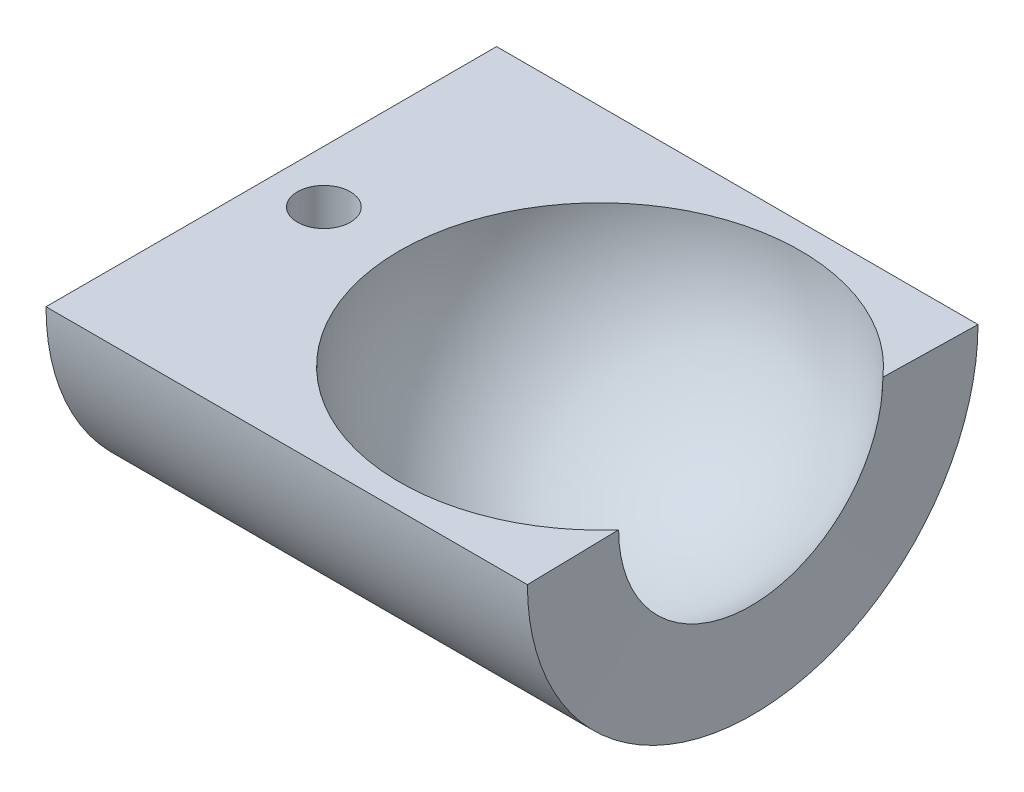
SolidWorks part; units mm, degrees
ref_plane "Alzado" through (0, 0, 0) normal (0, 0, 1) x (1, 0, 0)
ref_plane "Planta" through (0, 0, 0) normal (0, 1, 0) x (1, 0, 0)
ref_plane "Vista lateral" through (0, 0, 0) normal (1, 0, 0) x (0, 0, -1)
sketch "Croquis1" plane through (0, 0, 0) normal (0, 1, 0) x (1, 0, 0)
  line L0 (-12.5, 0) -> (-20.5, 0)
  line L1 (9.5211, 14.0495) -> (-20.5, 14.0495)
  line L3 (9.5211, 14.0495) -> (9.4, 8.2396)
  line L4 (-20.5, 14.0495) -> (-20.5, 0)
  arc A1 (9.4, 8.2396) -> (-12.5, 0) centre (0, 0) ccw
  dimension "D2" = 8
revolve "Revolución3" add sketch "Croquis1" angle 360 about L0
sketch "Croquis5" plane through (-20.5, 0, 0) normal (-1, 0, 0) x (0, 0, 1)
  line L2 (0, 0) -> (-16.8326, 0)
  line L3 (-16.8326, 0) -> (-16.8326, 15.4747)
  line L4 (-16.8326, 15.4747) -> (15.9251, 15.4747)
  line L5 (15.9251, 15.4747) -> (15.9251, 0)
  line L6 (15.9251, 0) -> (0, 0)
extrude "Cortar-Extruir3" cut sketch "Croquis5" against normal blind 45
sketch "Croquis6" plane through (0, 0, 0) normal (0, 1, 0) x (1, 0, 0)
  line L2 (-12.5, 0) -> (-20.5, 0) construction
  circle A0 centre (-17.2217, 0) radius 1.65
extrude "Cortar-Extruir4" cut sketch "Croquis6" against normal blind 20
